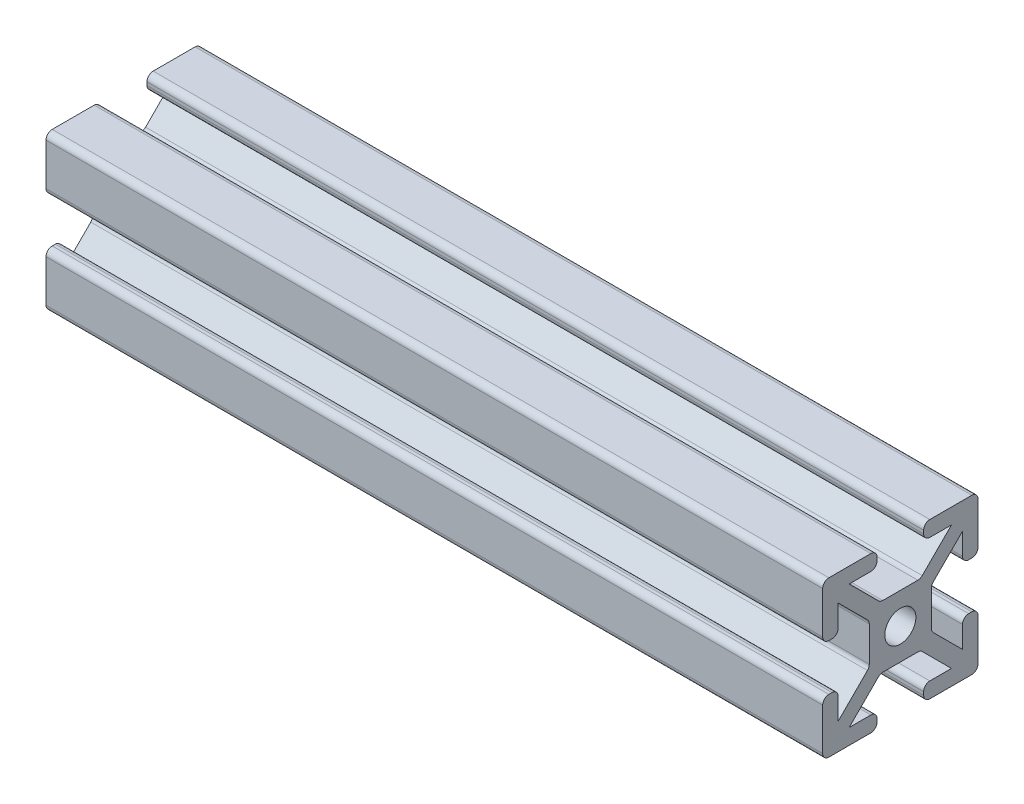
SolidWorks part; units mm, degrees
material "1060 Alloy"
ref_plane "Front Plane" through (0, 0, 0) normal (0, 0, 1) x (1, 0, 0)
ref_plane "Top Plane" through (0, 0, 0) normal (0, 1, 0) x (1, 0, 0)
ref_plane "Right Plane" through (0, 0, 0) normal (1, 0, 0) x (0, 0, -1)
sketch "Sketch1" plane through (0, 0, 0) normal (0, 1, 0) x (1, 0, 0)
  line L0 (0, 0) -> (100, 0)
other "Size 4X4 (1)"
ref_plane "Plane1" through (0, 0, 0) normal (1, 0, 0) x (0, 0, -1)
sketch "Sketch11" plane through (0, 0, 0) normal (1, 0, 0) x (0, 0, -1)
  line L0 (-3, 9.2) -> (-3, 8.8)
  line L1 (-2.2544, 4) -> (2.2544, 4)
  line L2 (-4, 2.2544) -> (-4, -2.2544)
  line L3 (-2.2544, -4) -> (2.2544, -4)
  line L4 (4, 2.2544) -> (4, -2.2544)
  line L7 (-6.5858, 8) -> (-3.8, 8)
  line L8 (-8, 6.5858) -> (-8, 3.8)
  line L9 (-6.5858, -8) -> (-3.8, -8)
  line L10 (8, 6.5858) -> (8, 3.8)
  line L12 (9.7657, -9.7657) -> (10, -10) construction
  line L13 (-9.2, 10) -> (-3.8, 10)
  line L14 (-10, 9.2) -> (-10, 3.8)
  line L15 (-9.2, -10) -> (-3.8, -10)
  line L16 (10, 9.2) -> (10, 3.8)
  line L17 (-10, 10) -> (-9.7657, 9.7657) construction
  line L18 (-10, -10) -> (-9.7657, -9.7657) construction
  line L21 (3, 9.2) -> (3, 8.8)
  line L22 (3, -9.2) -> (3, -8.8)
  line L23 (-3, -9.2) -> (-3, -8.8)
  line L24 (3.8, 10) -> (9.2, 10)
  line L25 (3.8, 8) -> (6.5858, 8)
  line L26 (-9.2, 3) -> (-8.8, 3)
  line L27 (9.2, 3) -> (8.8, 3)
  line L28 (9.2, -3) -> (8.8, -3)
  line L29 (-9.2, -3) -> (-8.8, -3)
  line L30 (-10, -3.8) -> (-10, -9.2)
  line L31 (-8, -3.8) -> (-8, -6.5858)
  line L32 (8, -3.8) -> (8, -6.5858)
  line L33 (10, -3.8) -> (10, -9.2)
  line L34 (3.8, -8) -> (6.5858, -8)
  line L35 (3.8, -10) -> (9.2, -10)
  line L36 (6.5858, 8) -> (2.8201, 4.2343)
  line L37 (8, 6.5858) -> (4.2343, 2.8201)
  line L38 (8, -6.5858) -> (4.2343, -2.8201)
  line L39 (6.5858, -8) -> (2.8201, -4.2343)
  line L40 (-6.5858, -8) -> (-2.8201, -4.2343)
  line L41 (-8, -6.5858) -> (-4.2343, -2.8201)
  line L42 (-8, 6.5858) -> (-4.2343, 2.8201)
  line L43 (-6.5858, 8) -> (-2.8201, 4.2343)
  line L47 (9.7657, 9.7657) -> (10, 10) construction
  circle A0 centre (0, 0) radius 2
  arc A1 (9.2, -3) -> (10, -3.8) centre (9.2, -3.8) cw
  arc A2 (8.8, -3) -> (8, -3.8) centre (8.8, -3.8) ccw
  arc A3 (3, -9.2) -> (3.8, -10) centre (3.8, -9.2) ccw
  arc A4 (3, -8.8) -> (3.8, -8) centre (3.8, -8.8) cw
  arc A5 (-3, -9.2) -> (-3.8, -10) centre (-3.8, -9.2) cw
  arc A6 (-3, -8.8) -> (-3.8, -8) centre (-3.8, -8.8) ccw
  arc A7 (-8.8, -3) -> (-8, -3.8) centre (-8.8, -3.8) cw
  arc A8 (-9.2, -3) -> (-10, -3.8) centre (-9.2, -3.8) ccw
  arc A9 (-10, -9.2) -> (-9.2, -10) centre (-9.2, -9.2) ccw
  arc A10 (9.2, -10) -> (10, -9.2) centre (9.2, -9.2) ccw
  arc A11 (9.2, 10) -> (10, 9.2) centre (9.2, 9.2) cw
  arc A12 (-9.2, 10) -> (-10, 9.2) centre (-9.2, 9.2) ccw
  arc A13 (9.2, 3) -> (10, 3.8) centre (9.2, 3.8) ccw
  arc A14 (8.8, 3) -> (8, 3.8) centre (8.8, 3.8) cw
  arc A15 (3, 9.2) -> (3.8, 10) centre (3.8, 9.2) cw
  arc A16 (3, 8.8) -> (3.8, 8) centre (3.8, 8.8) ccw
  arc A17 (-3, 9.2) -> (-3.8, 10) centre (-3.8, 9.2) ccw
  arc A18 (-3, 8.8) -> (-3.8, 8) centre (-3.8, 8.8) cw
  arc A19 (-8.8, 3) -> (-8, 3.8) centre (-8.8, 3.8) ccw
  arc A20 (-9.2, 3) -> (-10, 3.8) centre (-9.2, 3.8) cw
  arc A21 (-2.8201, 4.2343) -> (-2.2544, 4) centre (-2.2544, 4.8) ccw
  arc A22 (4.2343, 2.8201) -> (4, 2.2544) centre (4.8, 2.2544) ccw
  arc A23 (2.8201, 4.2343) -> (2.2544, 4) centre (2.2544, 4.8) cw
  arc A24 (4.2343, -2.8201) -> (4, -2.2544) centre (4.8, -2.2544) cw
  arc A25 (2.8201, -4.2343) -> (2.2544, -4) centre (2.2544, -4.8) ccw
  arc A26 (-2.8201, -4.2343) -> (-2.2544, -4) centre (-2.2544, -4.8) cw
  arc A27 (-4.2343, -2.8201) -> (-4, -2.2544) centre (-4.8, -2.2544) ccw
  arc A28 (-4.2343, 2.8201) -> (-4, 2.2544) centre (-4.8, 2.2544) cw
  point P7 (0, 0)
  point P10 (-2.5858, 4)
  point P53 (10, -3)
  point P56 (8, -3)
  point P59 (3, -10)
  point P62 (3, -8)
  point P65 (-3, -10)
  point P68 (-3, -8)
  point P71 (-8, -3)
  point P74 (-10, -3)
  point P89 (10, 3)
  point P92 (8, 3)
  point P95 (3, 10)
  point P98 (3, 8)
  point P101 (-3, 10)
  point P104 (-3, 8)
  point P107 (-8, 3)
  point P110 (-10, 3)
  point P116 (4, 2.5858)
  point P119 (2.5858, 4)
  point P122 (4, -2.5858)
  point P125 (2.5858, -4)
  point P128 (-2.5858, -4)
  point P131 (-4, -2.5858)
  point P134 (-4, 2.5858)
  dimension "D3" = 4
  dimension "D11" = 0.8
  dimension "D12" = 0.8
  dimension "D2" = 0.8
  dimension "D4" = 20
  dimension "D6" = 20
  dimension "D8" = 7
  dimension "D9" = 7
sketch "Sketch12" plane through (0, 0, -4) normal (0, 0, -1) x (-1, 0, 0)
  line L0 (-100, 0) -> (0, 0) construction
  line L1 (-100, -2.2544) -> (-100, 2.2544) construction
  line L2 (0, -2.2544) -> (0, 2.2544) construction
  circle A0 centre (-90, 0) radius 2.5
  dimension "D1" = 5
  dimension "D2" = 10
extrude "Cut-Extrude1" cut sketch "Sketch12" against normal blind 10
